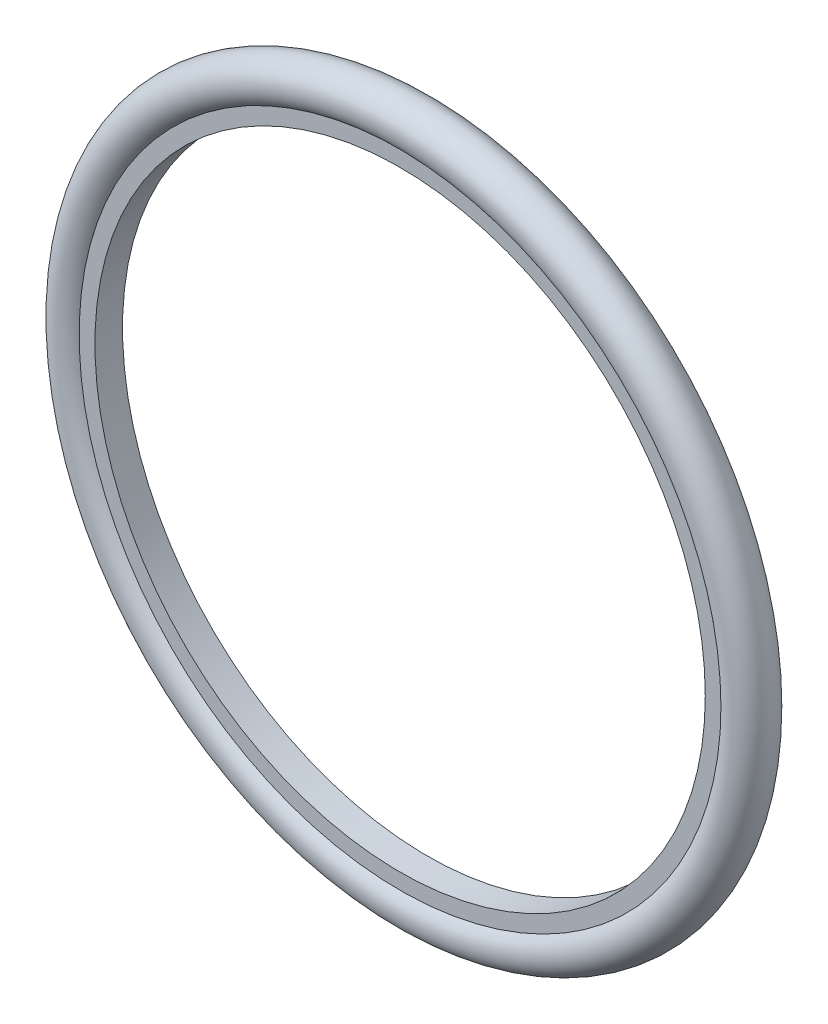
SolidWorks part; units mm, degrees
ref_plane "Alzado" through (0, 0, 0) normal (0, 0, 1) x (1, 0, 0)
ref_plane "Planta" through (0, 0, 0) normal (0, 1, 0) x (1, 0, 0)
ref_plane "Vista lateral" through (0, 0, 0) normal (1, 0, 0) x (0, 0, -1)
sketch "Croquis3" plane through (0, 0, 0) normal (1, 0, 0) x (0, 0, -1)
  line L0 (0, 0) -> (0, 317.5) construction
  line L1 (0, 0) -> (177.8, 0) construction
  line L2 (12.192, 269.875) -> (-12.192, 269.875)
  line L3 (12.192, 269.875) -> (12.192, 283.8125)
  line L5 (-12.192, 269.875) -> (-12.192, 283.8125)
  arc A0 (12.192, 283.8125) -> (-12.192, 283.8125) centre (0, 298.45) ccw
  dimension "D2" = 38.1
  dimension "D1" = 317.5
  dimension "D3" = 47.625
  dimension "D4" = 24.384
  dimension "D5" = 177.8
revolve "Revolución1" add sketch "Croquis3" angle 360 about L1
